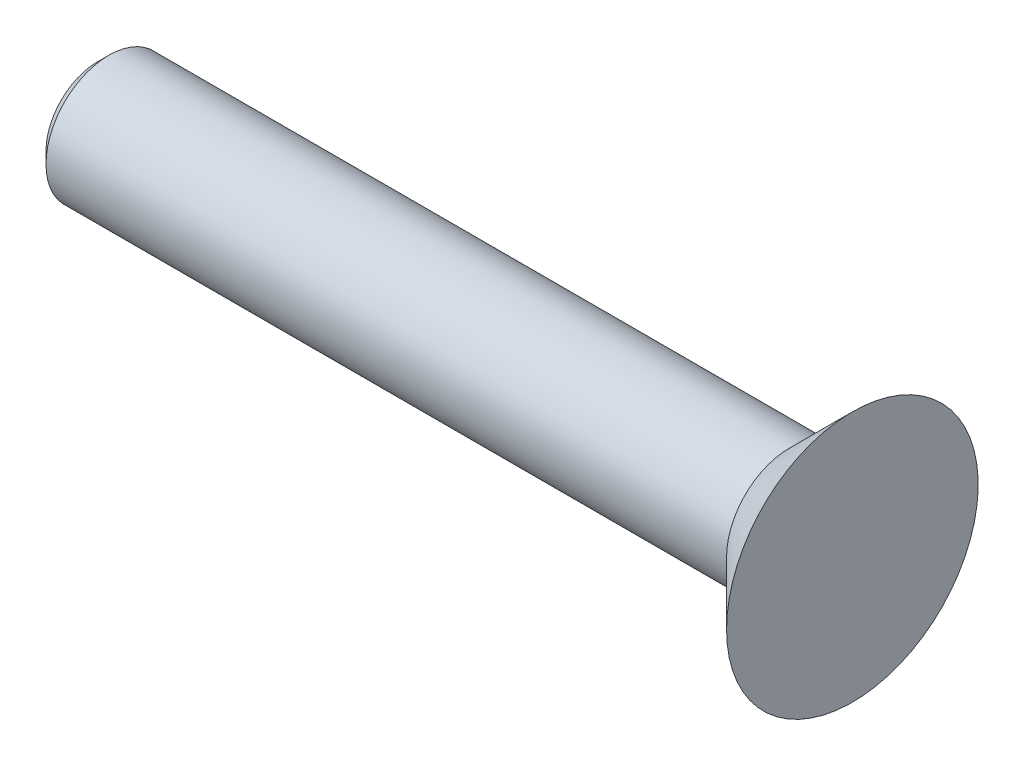
SolidWorks part; units mm, degrees
ref_plane "Plan de face" through (0, 0, 0) normal (0, 0, 1) x (1, 0, 0)
ref_plane "Plan de dessus" through (0, 0, 0) normal (0, 1, 0) x (1, 0, 0)
ref_plane "Plan de droite" through (0, 0, 0) normal (1, 0, 0) x (0, 0, -1)
sketch "Esquisse1" plane through (0, 0, 0) normal (0, 0, 1) x (1, 0, 0)
  line L0 (0, 0) -> (-15, 0)
  line L1 (-15, 0) -> (-15, 1.25)
  line L2 (-15, 1.25) -> (-1.25, 1.25)
  line L3 (-1.25, 1.25) -> (0, 2.5)
  line L4 (0, 2.5) -> (0, 0)
  line L5 (0, 0) -> (21.1509, 0) construction
  dimension "D1" = 45
  dimension "D2" = 1.25
  dimension "D3" = 2.5
  dimension "D4" = 15
revolve "Révolution1" add sketch "Esquisse1" angle 360 about L5
cosmetic thread "Représentation de filetage1" parameters "D2"=2.05
chamfer "Chanfrein1" distance 0.225 angle 45 1 edges at (-15, 0, 1.25)
